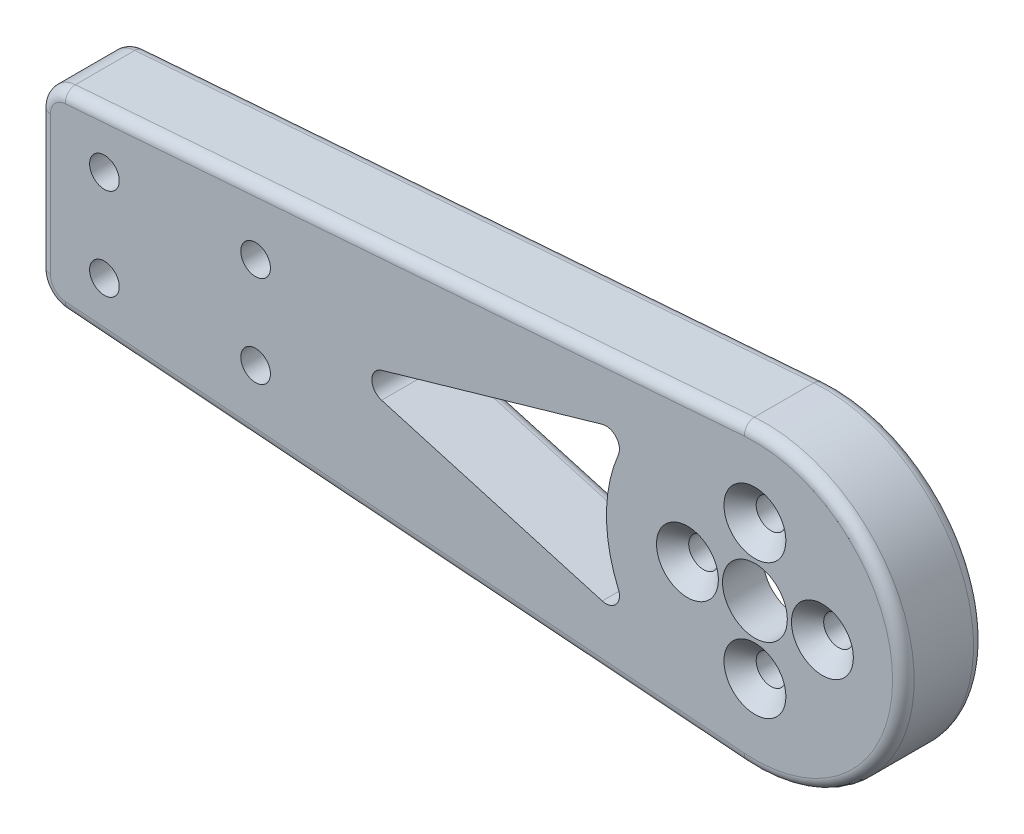
SolidWorks part; units mm, degrees
material "ABS"
ref_plane "Front Plane" through (0, 0, 0) normal (0, 0, 1) x (1, 0, 0)
ref_plane "Top Plane" through (0, 0, 0) normal (0, 1, 0) x (1, 0, 0)
ref_plane "Right Plane" through (0, 0, 0) normal (1, 0, 0) x (0, 0, -1)
sketch "Sketch1" plane through (0, 0, 0) normal (0, 0, 1) x (1, 0, 0)
  line L0 (0, 0) -> (-125, 0) construction
  line L1 (-125, -10) -> (-125, 10) construction
  line L2 (-2.0859, -27.4208) -> (-127.8793, -17.8515)
  line L3 (-132.5, 17.5) -> (-117.5, 17.5) construction
  line L4 (-132.5, 17.5) -> (-132.5, -17.5) construction
  line L5 (-132.5, -17.5) -> (-117.5, -17.5) construction
  line L6 (-117.5, 17.5) -> (-117.5, -17.5) construction
  line L7 (-132.5, 17.5) -> (-117.5, -17.5) construction
  line L8 (-132.5, -17.5) -> (-117.5, 17.5) construction
  line L9 (-132.5, -12.8659) -> (-132.5, 12.8659)
  line L10 (-127.8793, 17.8515) -> (-2.0859, 27.4208)
  circle A0 centre (0, 0) radius 6
  circle A1 centre (0, 0) radius 27.5 construction
  circle A2 centre (-125, 10) radius 2.5 construction
  circle A3 centre (-125, -10) radius 2.5 construction
  arc A4 (-2.0859, 27.4208) -> (-2.0859, -27.4208) centre (0, 0) cw
  arc A5 (-132.5, 12.8659) -> (-127.8793, 17.8515) centre (-127.5, 12.8659) cw
  arc A6 (-127.8793, -17.8515) -> (-132.5, -12.8659) centre (-127.5, -12.8659) cw
  point P8 (-125, 0)
  dimension "D1" = 12
  dimension "D2" = 55
  dimension "D5" = 5
  dimension "D6" = 5
  dimension "D9" = 5
  dimension "D3" = 125
  dimension "D4" = 20
  dimension "D7" = 35
  dimension "D8" = 15
  dimension "D10" = 132.5
extrude "Boss-Extrude1" add sketch "Sketch1" along normal mid plane 15
sketch "Sketch2" plane through (0, 0, -7.5) normal (0, 0, -1) x (-1, 0, 0)
  circle A0 centre (0, 0) radius 20
  dimension "D1" = 40
extrude "Cut-Extrude1" cut sketch "Sketch2" against normal blind 7.5
sketch "Sketch3" plane through (0, 0, 0) normal (0, 0, -1) x (-1, 0, 0)
  line L0 (20, 0) -> (-20, 0) construction
  line L1 (-20, 0) -> (0, 20) construction
  line L2 (0, 20) -> (0, -20) construction
  circle A0 centre (0, 0) radius 20 construction
  circle A1 centre (0, 0) radius 20 construction
  circle A2 centre (0, 12.5) radius 2.5
  circle A3 centre (0, -12.5) radius 2.5
  circle A4 centre (12.5, 0) radius 2.5
  circle A5 centre (-12.5, 0) radius 2.5
  dimension "D1" = 5
  dimension "D2" = 25
  dimension "D3" = 25
extrude "Cut-Extrude2" [suppressed] cut sketch "Sketch3" against normal blind 5
other "Graphic1" [suppressed]
other "Graphic (Closed) -1"
imported_body "Imported2" [suppressed]
other "Graphic2" [suppressed]
other "Graphic (Closed) -2"
imported_body "Imported3" [suppressed]
sketch "Sketch4" plane through (0, 0, -7.5) normal (0, 0, -1) x (-1, 0, 0)
  line L0 (0, 0) -> (132.5, 0) construction
  line L1 (132.5, 12.8659) -> (132.5, -12.8659) construction
  line L2 (28.2882, 14.1682) -> (69.1554, 2.4024)
  line L3 (69.1554, -2.4024) -> (28.2882, -14.1682)
  line L4 (2.0859, 27.4208) -> (127.8793, 17.8515) construction
  circle A0 centre (0, 0) radius 27.5 construction
  arc A2 (25.2968, -10.7853) -> (25.2968, 10.7853) centre (0, 0) ccw
  arc A3 (69.1554, 2.4024) -> (69.1554, -2.4024) centre (68.4638, 0) cw
  arc A4 (28.2882, -14.1682) -> (25.2968, -10.7853) centre (27.5965, -11.7658) cw
  arc A5 (28.2882, 14.1682) -> (25.2968, 10.7853) centre (27.5965, 11.7658) ccw
  point P19 (77.5, 0)
  point P22 (22.4795, -15.8405)
  point P25 (22.4795, 15.8405)
  dimension "D3" = 2.5
  dimension "D4" = 55
  dimension "D1" = 10
  dimension "D2" = 55
extrude "Cut-Extrude3" cut sketch "Sketch4" against normal through all
sketch "Sketch6" plane through (0, 0, -7.5) normal (0, 0, -1) x (-1, 0, 0)
  line L0 (-27.5, 0) -> (132.5, 0) construction
  line L1 (132.5, 12.8659) -> (132.5, -12.8659) construction
  line L2 (58.6316, 10.6353) -> (79.3555, 4.6689)
  line L3 (82.5472, 7.0713) -> (82.5472, 11.4613)
  line L4 (80.2368, 13.9541) -> (59.5129, 15.5306)
  line L5 (2.0859, 27.4208) -> (127.8793, 17.8515) construction
  line L6 (69.1554, 2.4024) -> (28.2882, 14.1682) construction
  line L7 (82.5472, -7.0713) -> (82.5472, -11.4613)
  line L8 (58.6316, -10.6353) -> (79.3555, -4.6689)
  line L9 (80.2368, -13.9541) -> (59.5129, -15.5306)
  arc A0 (2.0859, 27.4208) -> (2.0859, -27.4208) centre (0, 0) ccw construction
  arc A1 (82.5472, 11.4613) -> (80.2368, 13.9541) centre (80.0472, 11.4613) ccw
  arc A2 (79.3555, 4.6689) -> (82.5472, 7.0713) centre (80.0472, 7.0713) ccw
  arc A3 (58.6316, 10.6353) -> (59.5129, 15.5306) centre (59.3233, 13.0378) cw
  arc A4 (79.3555, -4.6689) -> (82.5472, -7.0713) centre (80.0472, -7.0713) cw
  arc A5 (82.5472, -11.4613) -> (80.2368, -13.9541) centre (80.0472, -11.4613) cw
  arc A6 (58.6316, -10.6353) -> (59.5129, -15.5306) centre (59.3233, -13.0378) ccw
  point P18 (82.5472, 3.75)
  dimension "D4" = 2.5
  dimension "D1" = 5
  dimension "D2" = 7.5
  dimension "D3" = 7.5
extrude "Cut-Extrude5" cut sketch "Sketch6" against normal blind 10
sketch "Sketch7" plane through (0, 0, -7.5) normal (0, 0, -1) x (-1, 0, 0)
  line L0 (132.5, 0) -> (70.9638, 0) construction
  line L1 (132.5, 12.8659) -> (132.5, -12.8659) construction
  arc A0 (69.1554, -2.4024) -> (69.1554, 2.4024) centre (68.4638, 0) ccw construction
sketch "Sketch10" plane through (0, 0, -7.5) normal (0, 0, -1) x (-1, 0, 0)
  line L0 (69.1554, 2.4024) -> (28.2882, 14.1682) construction
  line L1 (28.2882, -14.1682) -> (69.1554, -2.4024) construction
  line L2 (49.3383, 8.1078) -> (54.6035, 6.5919)
  line L3 (54.6035, -6.5919) -> (49.3383, -8.1078)
  circle A0 centre (0, 0) radius 50 construction
  arc A1 (49.3383, 8.1078) -> (49.3383, -8.1078) centre (0, 0) cw
  circle A2 centre (0, 0) radius 55 construction
  arc A3 (54.6035, 6.5919) -> (54.6035, -6.5919) centre (0, 0) cw
  dimension "D1" = 100
  dimension "D2" = 5
sketch "Sketch9" plane through (0, 0, 0) normal (0, 0, 1) x (1, 0, 0)
  line L0 (-2.0859, 27.4208) -> (-7.4508, 32.0271)
  line L1 (-7.4508, 32.0271) -> (-122.1195, 23.3041)
  line L2 (-122.1195, 23.3041) -> (-126.7258, 17.9392)
  line L3 (-2.0859, 27.4208) -> (-127.8793, 17.8515) construction
  line L4 (-126.7258, 17.9392) -> (-2.0859, 27.4208)
  arc A0 (-2.0859, -27.4208) -> (-2.0859, 27.4208) centre (0, 0) ccw construction
  dimension "D1" = 45
  dimension "D2" = 45
  dimension "D3" = 5
  dimension "D4" = 125
extrude "Boss-Extrude2" [suppressed] add sketch "Sketch9" along normal mid plane 10
fillet "Fillet4" radius 2 30 edges at (-70.9638, 0, -7.5) (-48.7218, -8.2853, -7.5) (-81.8808, 13.1607, -7.5) (-82.5472, 9.2663, -7.5) (-81.5507, 5.0739, -7.5) (-68.9936, 7.6521, -7.5) (-56.8628, 13.4807, -7.5) (-25.7237, 13.4218, -7.5) (-48.7218, 8.2853, -7.5) (-25.7237, -13.4218, -7.5) (-69.8749, 14.7423, -7.5) (-27.5, 0, -7.5) (-64.9826, -22.6361, 7.5) (-131.1672, -16.2647, 7.5) (-132.5, 0, 7.5) (-131.1672, 16.2647, 7.5) (-64.9826, 22.6361, 7.5) (27.5, 0, 7.5) (27.5, 0, -7.5) (-64.9826, -22.6361, -7.5) (-131.1672, -16.2647, -7.5) (-132.5, 0, -7.5) (-131.1672, 16.2647, -7.5) (-64.9826, 22.6361, -7.5) (-81.5507, -5.0739, -7.5) (-82.5472, -9.2663, -7.5) (-81.8808, -13.1607, -7.5) (-69.8749, -14.7423, -7.5) (-56.8628, -13.4807, -7.5) (-68.9936, -7.6521, -7.5)
hole_wizard "CSK for M5 Hex Socket Countersunk Head Screw1" positions "Sketch11" profile "Sketch12" countersink size "M5" standard "DIN" end condition through all
sketch "Sketch11" plane through (0, 0, 7.5) normal (0, 0, 1) x (1, 0, 0)
  circle A0 centre (0, 0) radius 12.5 construction
  point P4 (0, 12.5)
  point P10 (12.5, 0)
  point P11 (0, -12.5)
  point P12 (-12.5, 0)
  dimension "D1" = 25
  dimension "D2" = 4
sketch "Sketch12" plane through (-12.5, 0, 7.5) normal (1, 0, 0) x (0, -1, 0)
  line L0 (0, 0) -> (0, 15)
  line L1 (0, 15) -> (2.75, 15)
  line L2 (2.75, 15) -> (2.75, 2.985)
  line L3 (2.75, 2.985) -> (5.735, 0)
  line L5 (5.735, 0) -> (0, 0)
  line L6 (-2.75, 2.985) -> (-5.735, 0) construction
  line L11 (0, -6.35) -> (0, 107.95) construction
  dimension "Thru Hole Dia." = 5.5
  dimension "Thru Hole Depth" = 15
  dimension "Near C'Sink Dia." = 11.47
  dimension "Near C'Sink Angle" = 90
sketch "Sketch15" plane through (0, 0, -7.5) normal (0, 0, -1) x (-1, 0, 0)
  line L0 (132.5, 0) -> (70.9638, 0) construction
  line L1 (130.5, -12.8659) -> (130.5, 12.8659) construction
  line L3 (92.5, -31.994) -> (92.5, 55.7872) construction
  point P0 (92.5, 8.5)
  dimension "D1" = 8.5
  dimension "D2" = 38
hole_wizard "CSK for M5 Hex Socket Countersunk Head Screw2" positions "Sketch15" profile "Sketch14" countersink size "M5" standard "DIN" end condition through all
sketch "Sketch14" plane through (-92.5, 8.5, -7.5) normal (1, 0, 0) x (0, 1, 0)
  line L0 (0, 0) -> (0, 15)
  line L1 (0, 15) -> (2.75, 15)
  line L2 (2.75, 15) -> (2.75, 2.985)
  line L3 (2.75, 2.985) -> (5.735, 0)
  line L5 (5.735, 0) -> (0, 0)
  line L6 (-2.75, 2.985) -> (-5.735, 0) construction
  line L11 (0, -6.35) -> (0, 107.95) construction
  dimension "Thru Hole Dia." = 5.5
  dimension "Thru Hole Depth" = 15
  dimension "Near C'Sink Dia." = 11.47
  dimension "Near C'Sink Angle" = 90
pattern_linear "LPattern1" count 2 spacing 28 along (-1, 0, 0) count 2 spacing 17 along (0, -1, 0) of "CSK for M5 Hex Socket Countersunk Head Screw2"
equation "\"25mmmm\"=20"
